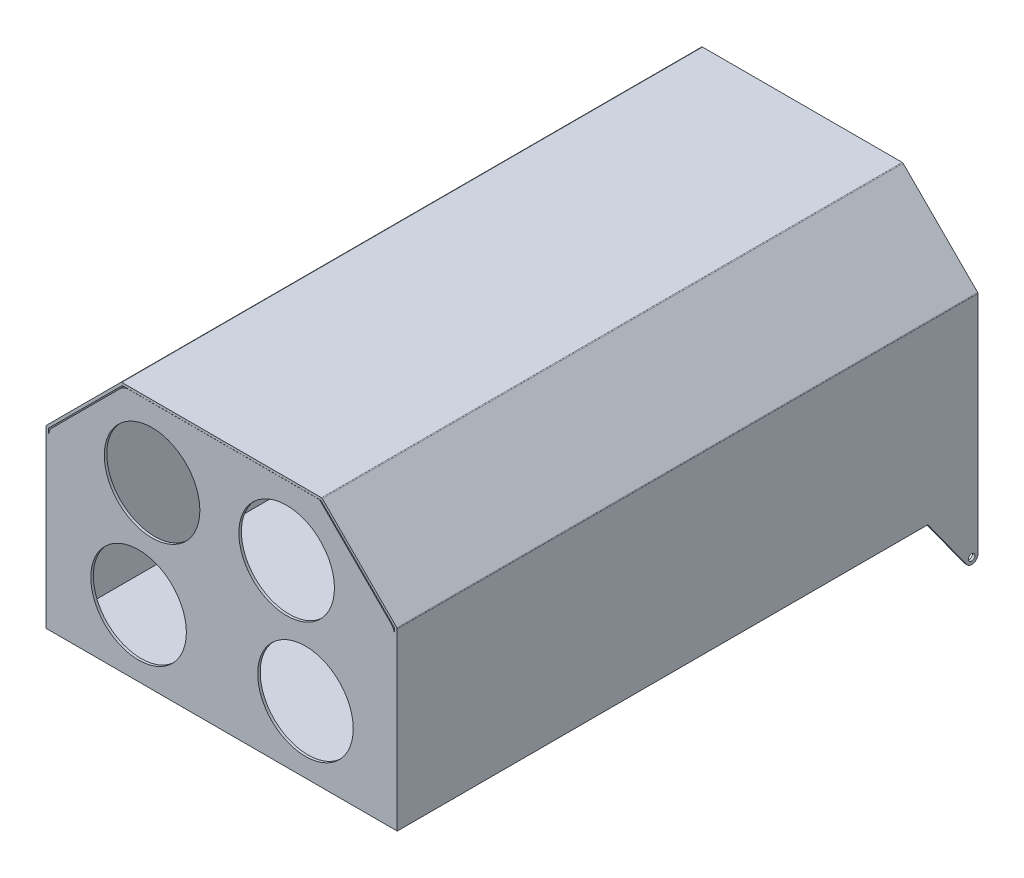
SolidWorks part; units mm, degrees
ref_plane "Front Plane" through (0, 0, 0) normal (0, 0, 1) x (1, 0, 0)
ref_plane "Top Plane" through (0, 0, 0) normal (0, 1, 0) x (1, 0, 0)
ref_plane "Right Plane" through (0, 0, 0) normal (1, 0, 0) x (0, 0, -1)
sketch "Sketch1" plane through (0, 0, 0) normal (0, 0, 1) x (1, 0, 0)
  line L0 (-169.6578, 59.751) -> (-110.2436, 119.1652)
  line L1 (-109.5365, 119.4581) -> (49.635, 119.4581)
  line L2 (-169.9507, 59.0439) -> (-169.9507, -80.5409)
  line L3 (-169.9497, -80.5419) -> (110.0483, -80.5419)
  line L4 (110.0493, 59.0439) -> (110.0493, -80.5409)
  line L5 (50.3422, 119.1652) -> (109.7564, 59.751)
  arc A0 (109.7564, 59.751) -> (110.0493, 59.0439) centre (109.0493, 59.0439) cw
  arc A1 (50.3422, 119.1652) -> (49.635, 119.4581) centre (49.635, 118.4581) ccw
  arc A2 (-169.6578, 59.751) -> (-169.9507, 59.0439) centre (-168.9507, 59.0439) ccw
  arc A3 (-110.2436, 119.1652) -> (-109.5365, 119.4581) centre (-109.5365, 118.4581) cw
  arc A4 (110.0483, -80.5419) -> (110.0493, -80.5409) centre (110.0483, -80.5409) ccw
  arc A5 (-169.9507, -80.5409) -> (-169.9497, -80.5419) centre (-169.9497, -80.5409) ccw
  point P0 (-169.9507, 119.4581)
  point P3 (110.0493, 119.4581)
  point P10 (110.0493, 59.4581)
  point P13 (50.0493, 119.4581)
  point P16 (-169.9507, 59.4581)
  point P19 (-109.9507, 119.4581)
  point P22 (110.0493, -80.5419)
  point P25 (-169.9507, -80.5419)
  dimension "D3" = 1
  dimension "D4" = 0.001
  dimension "D1" = 200
  dimension "D2" = 280
extrude "Boss-Extrude1" add sketch "Sketch1" along normal blind 463
shell "Shell2" thickness 2
sketch "Sketch2" plane through (110.0493, 0, 0) normal (1, 0, 0) x (0, 0, -1)
  line L0 (-40, -80.5409) -> (-9.0255, -123.5065)
  line L1 (-463, -80.5409) -> (0, -80.5409) construction
  line L3 (0, -120.5409) -> (0, -80.5409)
  line L4 (0, -80.5409) -> (-40, -80.5409)
  arc A0 (-9.0255, -123.5065) -> (0, -120.5409) centre (-5, -120.5409) ccw
  circle A1 centre (-5, -120.5409) radius 2.55
  dimension "D3" = 10
  dimension "D1" = 40
  dimension "D2" = 40
extrude "Boss-Extrude2" add sketch "Sketch2" against normal blind 2
ref_plane "Plane1" through (-30, 0, 0) normal (1, 0, 0) x (0, 0, -1)
ref_plane "Plane2" through (-29.9507, 0, 0) normal (1, 0, 0) x (0, 0, -1)
ref_plane "Plane3" through (-49.9507, 0, 0) normal (1, 0, 0) x (0, 0, -1)
mirror "Mirror1" about plane through (-29.9507, 0, 0) normal (1, 0, 0) of "Boss-Extrude2"
sketch "Sketch4" plane through (-49.9507, 0, 0) normal (1, 0, 0) x (0, 0, -1)
  line L0 (-352.327, -122.9663) -> (-377.5712, -80.5409)
  line L1 (-463, -80.5409) -> (-40, -80.5409) construction
  line L2 (-377.5712, -80.5409) -> (-309.674, -80.5409)
  line L3 (-309.674, -80.5409) -> (-336.8995, -123.5893)
  circle A0 centre (-344.4334, -118.8246) radius 5.25
  arc A1 (-352.327, -122.9663) -> (-336.8995, -123.5893) centre (-344.4334, -118.8246) ccw
extrude "Boss-Extrude3" add sketch "Sketch4" against normal blind 2
mirror "Mirror2" about plane through (-29.9507, 0, 0) normal (1, 0, 0) of "Boss-Extrude3"
sketch "Sketch5" plane through (0, 0, 463) normal (0, 0, 1) x (1, 0, 0)
  line L0 (-165.0218, 60.3) -> (-110.8797, 114.4421)
  line L1 (-167.9507, -78.5419) -> (108.0493, -78.5419)
  line L2 (-167.9507, -78.5419) -> (-167.9507, 53.2289)
  line L3 (-103.8086, 117.3711) -> (48.0493, 117.3711)
  line L4 (108.0493, -78.5419) -> (108.0493, 53.2289)
  line L5 (48.0493, 117.3711) -> (105.1203, 60.3)
  arc A0 (-110.8797, 114.4421) -> (-103.8086, 117.3711) centre (-103.8086, 107.3711) cw
  arc A1 (-165.0218, 60.3) -> (-167.9507, 53.2289) centre (-157.9507, 53.2289) ccw
  arc A2 (105.1203, 60.3) -> (108.0493, 53.2289) centre (98.0493, 53.2289) cw
  point P1 (108.0493, 117.3711)
  point P2 (-167.9507, 117.3711)
  point P11 (-107.9507, 117.3711)
  point P14 (-167.9507, 57.3711)
  point P17 (108.0493, 57.3711)
  dimension "D1" = 10
extrude "Boss-Extrude4" add sketch "Sketch5" against normal blind 2
sketch "Sketch6" plane through (0, 0, 463) normal (0, 0, 1) x (1, 0, 0)
  circle A0 centre (36.8951, -27.4548) radius 38.1
  circle A1 centre (-96.1444, -27.4548) radius 38.1
  circle A2 centre (-85.3839, 62.2164) radius 38.1
  circle A3 centre (21.8955, 62.2164) radius 38.1
extrude "Cut-Extrude1" cut sketch "Sketch6" against normal blind 2
